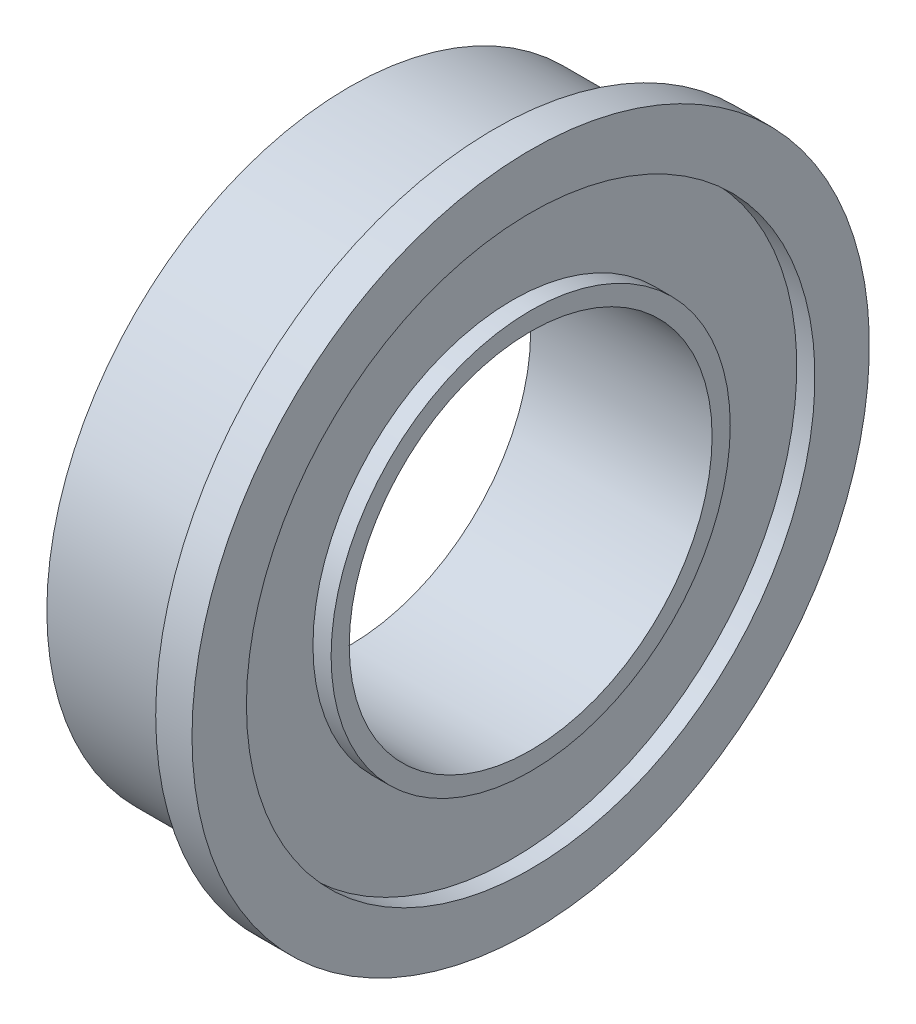
SolidWorks part; units mm, degrees
material "AISI 304"
ref_plane "Front Plane" through (0, 0, 0) normal (0, 0, 1) x (1, 0, 0)
ref_plane "Top Plane" through (0, 0, 0) normal (0, 1, 0) x (1, 0, 0)
ref_plane "Right Plane" through (0, 0, 0) normal (1, 0, 0) x (0, 0, -1)
sketch "Sketch1" plane through (0, 0, 0) normal (0, 0, 1) x (1, 0, 0)
  line L0 (0, 5.6) -> (0, 5)
  line L1 (0, 5.6) -> (0.6, 5.6)
  line L2 (0.6, 5.6) -> (0.6, 4.7)
  line L3 (0.6, 3) -> (-2.4, 3)
  line L4 (-2.4, 3) -> (-2.4, 3.3)
  line L5 (-2.4, 5) -> (0, 5)
  line L6 (-9.6318, 0) -> (7.0903, 0) construction
  line L7 (-2.4, 4.7) -> (-2.1, 4.7)
  line L8 (-2.1, 4.7) -> (-2.1, 3.3)
  line L9 (-2.1, 3.3) -> (-2.4, 3.3)
  line L10 (0.6, 4.7) -> (0.3, 4.7)
  line L11 (0.3, 4.7) -> (0.3, 3.3)
  line L12 (0.3, 3.3) -> (0.6, 3.3)
  line L13 (-2.4, 4.7) -> (-2.4, 5)
  line L14 (0.6, 3.3) -> (0.6, 3)
  dimension "D1" = 6
  dimension "D2" = 10
  dimension "D3" = 6.6
  dimension "D4" = 11.2
  dimension "D5" = 0.6
  dimension "D6" = 3
  dimension "D7" = 0.3
revolve "Revolve1" add sketch "Sketch1" angle 360 about L6
